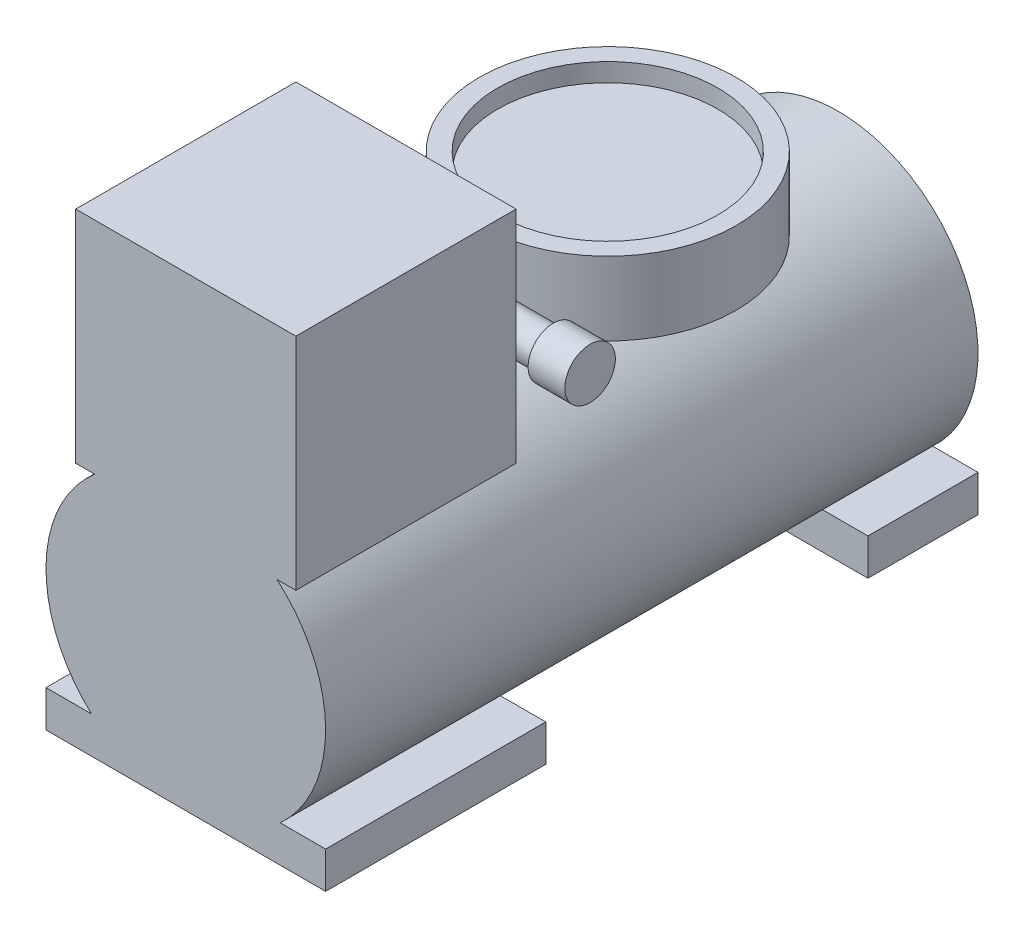
SolidWorks part; units mm, degrees
ref_plane "Front Plane" through (0, 0, 0) normal (0, 0, 1) x (1, 0, 0)
ref_plane "Top Plane" through (0, 0, 0) normal (0, 1, 0) x (1, 0, 0)
ref_plane "Right Plane" through (0, 0, 0) normal (1, 0, 0) x (0, 0, -1)
sketch "Sketch1" plane through (0, 0, 0) normal (0, 0, 1) x (1, 0, 0)
  circle A0 centre (0, 0) radius 38.1
  dimension "D1" = 76.2
extrude "Boss-Extrude1" add sketch "Sketch1" along normal blind 177.8
sketch "Sketch2" plane through (0, 0, 177.8) normal (0, 0, 1) x (1, 0, 0)
  line L0 (0, 0) -> (0, 83.3241) construction
  line L1 (0, -38.1) -> (67.8705, -38.1) construction
  line L2 (-30, 28.9) -> (30, 28.9)
  line L3 (-30, 28.9) -> (-30, 88.9)
  line L4 (-30, 88.9) -> (30, 88.9)
  line L5 (30, 28.9) -> (30, 88.9)
  line L6 (-30, 28.9) -> (30, 88.9) construction
  line L7 (-30, 88.9) -> (30, 28.9) construction
  line L8 (0, 0) -> (0, -38.1) construction
  line L10 (-38.1, -28.1) -> (38.1, -28.1)
  line L11 (-38.1, -28.1) -> (-38.1, -38.1)
  line L12 (-38.1, -38.1) -> (38.1, -38.1)
  line L13 (38.1, -28.1) -> (38.1, -38.1)
  circle A0 centre (0, 0) radius 38.1 construction
  point P3 (0, 58.9)
  dimension "D1" = 127
  dimension "D2" = 60
  dimension "D3" = 60
  dimension "D4" = 76.2
  dimension "D5" = 38.1
  dimension "D6" = 10
extrude "Boss-Extrude2" add sketch "Sketch2" against normal blind 60
sketch "Sketch3" plane through (0, 0, 117.8) normal (0, 0, -1) x (-1, 0, 0)
  circle A0 centre (0, 50) radius 5
  dimension "D1" = 10
  dimension "D2" = 50
extrude "Boss-Extrude3" add sketch "Sketch3" along normal blind 20
sketch "Sketch4" plane through (0, 0, 97.8) normal (0, 0, -1) x (-1, 0, 0)
  line L1 (-35, 40) -> (35, 40)
  line L2 (-35, 40) -> (-35, 60)
  line L3 (-35, 60) -> (35, 60)
  line L4 (35, 40) -> (35, 60)
  line L5 (-35, 40) -> (35, 60) construction
  line L6 (-35, 60) -> (35, 40) construction
  point P0 (0, 50)
  dimension "D1" = 70
  dimension "D2" = 20
extrude "Boss-Extrude4" add sketch "Sketch4" along normal blind 70
sketch "Sketch5" plane through (0, 60, 0) normal (0, 1, 0) x (1, 0, 0)
  line L0 (-5, -106.1773) -> (-48.7419, -106.1773)
  line L3 (-5, -106.1773) -> (-5, -97.441)
  line L4 (48.7419, -106.1773) -> (5, -106.1773)
  line L5 (48.7419, -106.1773) -> (48.7419, -19.4227)
  line L6 (48.7419, -19.4227) -> (-48.7419, -19.4227)
  line L7 (-48.7419, -106.1773) -> (-48.7419, -19.4227)
  line L10 (-5, -97.8) -> (-5, -117.8) construction
  line L12 (5, -97.441) -> (5, -106.1773)
  arc A0 (5, -97.441) -> (-5, -97.441) centre (0, -62.8) ccw
extrude "Cut-Extrude3" cut sketch "Sketch5" against normal blind 22
sketch "Sketch6" plane through (0, 60, 0) normal (0, 1, 0) x (1, 0, 0)
  circle A0 centre (0, -62.8) radius 30
  dimension "D1" = 60
extrude "Cut-Extrude4" cut sketch "Sketch6" against normal blind 5
sketch "Sketch7" plane through (0, 0, 0) normal (0, 0, -1) x (-1, 0, 0)
  line L0 (38.1, -28.1) -> (25.7294, -28.1) construction
  line L1 (0, -38.1) -> (38.1, -38.1) construction
  line L2 (38.1, -38.1) -> (38.1, -28.1) construction
  line L3 (-38.1, -38.1) -> (0, -38.1) construction
  line L4 (-25.7294, -28.1) -> (-38.1, -28.1) construction
  line L5 (-38.1, -28.1) -> (-38.1, -38.1) construction
  line L6 (38.1, -28.1) -> (25.7294, -28.1)
  line L7 (0, -38.1) -> (38.1, -38.1)
  line L8 (38.1, -38.1) -> (38.1, -28.1)
  line L9 (-38.1, -38.1) -> (0, -38.1)
  line L10 (-25.7294, -28.1) -> (-38.1, -28.1)
  line L11 (-38.1, -28.1) -> (-38.1, -38.1)
  arc A0 (0, -38.1) -> (25.7294, -28.1) centre (0, 0) ccw construction
  circle A1 centre (0, 0) radius 38.1
  circle A2 centre (0, 0) radius 38.1
  arc A3 (-25.7294, -28.1) -> (0, -38.1) centre (0, 0) ccw construction
  arc A4 (0, -38.1) -> (25.7294, -28.1) centre (0, 0) ccw
  arc A5 (-25.7294, -28.1) -> (0, -38.1) centre (0, 0) ccw
  circle M2 centre (0, 0) radius 38.1
  dimension "D1" = 0
extrude "Boss-Extrude5" add sketch "Sketch7" against normal blind 30 contours L10 L11 L9 M2 | L7 L8 L6 M2
sketch "Sketch8" plane through (0, 0, 0) normal (1, 0, 0) x (0, 0, -1)
  line L0 (-97.441, 50) -> (-117.8, 50) construction
  line L1 (-97.441, 40) -> (-97.441, 60) construction
  line L2 (-117.8, 28.9) -> (-117.8, 88.9) construction
  circle A0 centre (-107.6205, 50) radius 5
extrude "Boss-Extrude6" add sketch "Sketch8" along normal blind 40
sketch "Sketch9" plane through (40, 0, 0) normal (1, 0, 0) x (0, 0, -1)
  circle A0 centre (-107.6205, 50) radius 6.8955
extrude "Boss-Extrude7" add sketch "Sketch9" against normal blind 10
